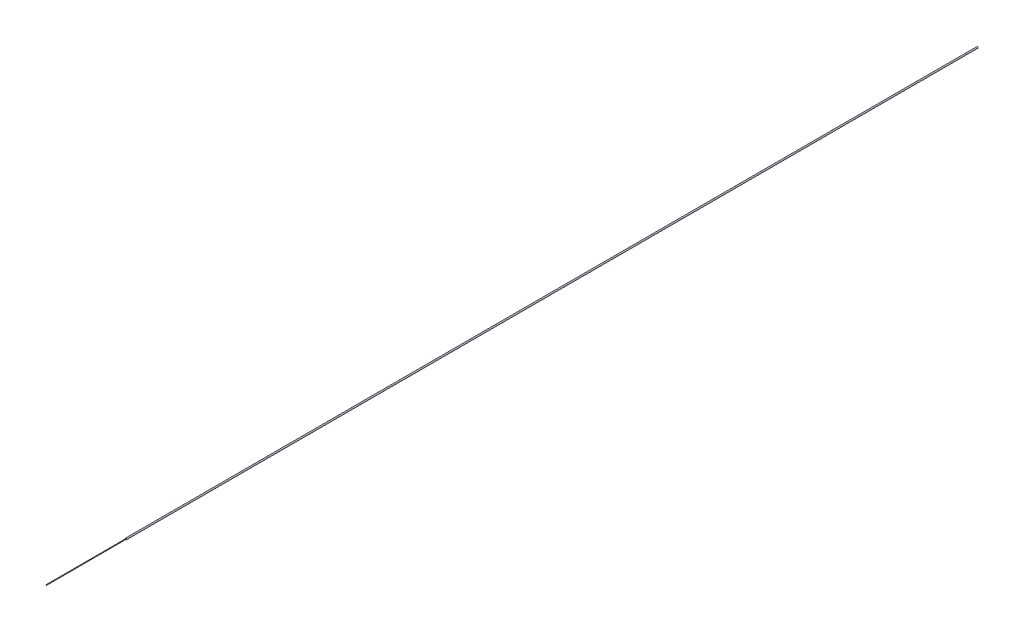
SolidWorks part; units mm, degrees
ref_plane "Front Plane" through (0, 0, 0) normal (0, 0, 1) x (1, 0, 0)
ref_plane "Top Plane" through (0, 0, 0) normal (0, 1, 0) x (1, 0, 0)
ref_plane "Right Plane" through (0, 0, 0) normal (1, 0, 0) x (0, 0, -1)
sketch "Sketch1" plane through (0, 0, 0) normal (0, 0, 1) x (1, 0, 0)
  circle A0 centre (0, 0) radius 1.143
  dimension "D1" = 2.286
extrude "Boss-Extrude1" add sketch "Sketch1" along normal blind 1389 contours A0
sketch "Sketch4" plane through (0, 0, 1389) normal (0, 0, -1) x (-1, 0, 0)
  circle A0 centre (0, 0) radius 0.5
  dimension "D1" = 1
sketch3d "3DSketch1"
  spline S0 degree 1 poles (0, 0, 1389) (0.1818, 0, 1518.9999) knots 0 0 1 1
  dimension "D1" = 130
sweep "Sweep2" add profiles "Sketch4" path "3DSketch1"
